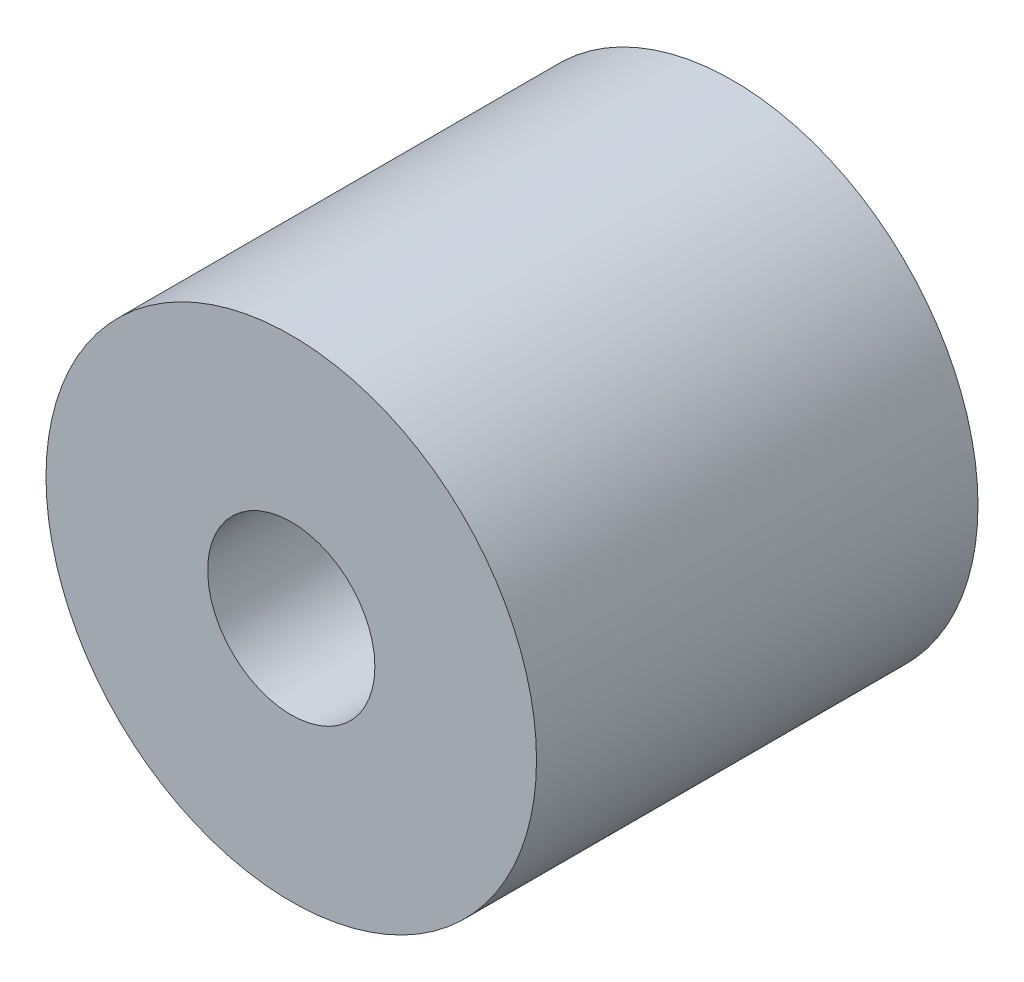
SolidWorks part; units mm, degrees
ref_plane "Plano frontal" through (0, 0, 0) normal (0, 0, 1) x (1, 0, 0)
ref_plane "Plano superior" through (0, 0, 0) normal (0, 1, 0) x (1, 0, 0)
ref_plane "Plano direito" through (0, 0, 0) normal (1, 0, 0) x (0, 0, -1)
sketch "Esboço1" plane through (0, 0, 0) normal (0, 0, 1) x (1, 0, 0)
  circle A0 centre (0, 0) radius 1.875
  circle A1 centre (0, 0) radius 5.5
  dimension "D1" = 11
  dimension "D2" = 3.75
extrude "Ressalto-extrusão1" add sketch "Esboço1" along normal blind 9.9
